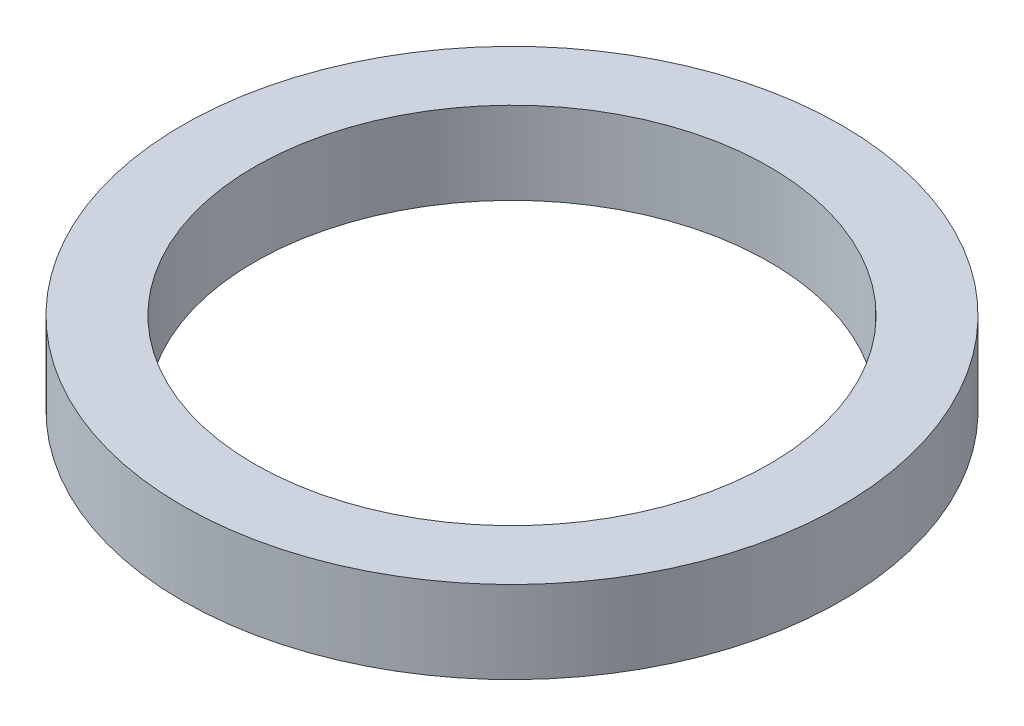
SolidWorks part; units mm, degrees
ref_plane "Front Plane" through (0, 0, 0) normal (0, 0, 1) x (1, 0, 0)
ref_plane "Top Plane" through (0, 0, 0) normal (0, 1, 0) x (1, 0, 0)
ref_plane "Right Plane" through (0, 0, 0) normal (1, 0, 0) x (0, 0, -1)
sketch "Sketch1" plane through (0, 0, 0) normal (0, 1, 0) x (1, 0, 0)
  circle A0 centre (0, 0) radius 12.5
  circle A1 centre (0, 0) radius 16
  dimension "D1" = 32
  dimension "D2" = 25
extrude "Boss-Extrude1" add sketch "Sketch1" along normal blind 4
